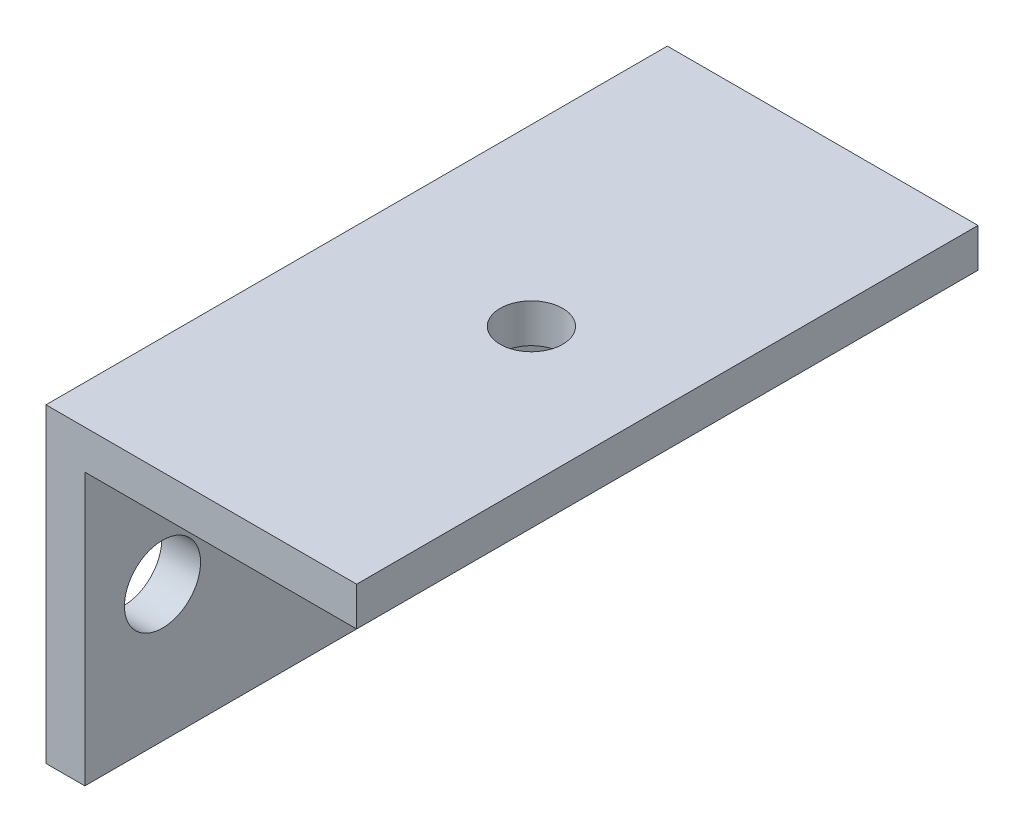
SolidWorks part; units mm, degrees
ref_plane "Front Plane" through (0, 0, 0) normal (0, 0, 1) x (1, 0, 0)
ref_plane "Top Plane" through (0, 0, 0) normal (0, 1, 0) x (1, 0, 0)
ref_plane "Right Plane" through (0, 0, 0) normal (1, 0, 0) x (0, 0, -1)
sketch "Sketch3" plane through (0, 0, 0) normal (0, 0, 1) x (1, 0, 0)
  line L0 (0, 0) -> (0, 25.4)
  line L1 (0, 25.4) -> (25.4, 25.4)
  line L2 (25.4, 25.4) -> (25.4, 22.225)
  line L3 (25.4, 22.225) -> (3.175, 22.225)
  line L4 (3.175, 22.225) -> (3.175, 0)
  line L5 (3.175, 0) -> (0, 0)
  dimension "D1" = 25.4
  dimension "D2" = 3.175
extrude "Boss-Extrude1" add sketch "Sketch3" along normal blind 50.8
sketch "Sketch6" plane through (3.175, 0, 0) normal (1, 0, 0) x (0, 0, -1)
  line L3 (-50.8, 11.1125) -> (0, 11.1125) construction
  line L4 (-50.8, 0) -> (-50.8, 22.225) construction
  line L5 (0, 0) -> (0, 22.225) construction
  circle A0 centre (-44.45, 11.1125) radius 3.1115
  circle A1 centre (-6.35, 11.1125) radius 3.1115
  dimension "D1" = 6.223
  dimension "D2" = 6.35
  dimension "D3" = 6.223
  dimension "D4" = 6.35
extrude "Cut-Extrude1" cut sketch "Sketch6" against normal through all
sketch "Sketch7" plane through (0, 22.225, 0) normal (0, -1, 0) x (-1, 0, 0)
  line L0 (-14.2875, -50.8) -> (-14.2875, 0) construction
  line L5 (-3.175, -50.8) -> (-25.4, -50.8) construction
  line L6 (-3.175, 0) -> (-25.4, 0) construction
hole_wizard "#10 Clearance Hole2" positions "Sketch9" profile "Sketch8" hole size "#10" standard "ANSI Inch" end condition through all
sketch "Sketch9" plane through (0, 22.225, 0) normal (0, -1, 0) x (-1, 0, 0)
  point P0 (-14.2875, -25.4)
  dimension "D1" = 25.4
sketch "Sketch8" plane through (14.2875, 22.225, 25.4) normal (1, 0, 0) x (0, 0, -1)
  line L0 (0, 0) -> (0, 3.175)
  line L1 (0, 3.175) -> (2.5527, 3.175)
  line L2 (2.5527, 3.175) -> (2.5527, 0)
  line L5 (2.5527, 0) -> (0, 0)
  line L11 (0, -6.35) -> (0, 107.95) construction
  dimension "Thru Hole Dia." = 5.1054
  dimension "Thru Hole Depth" = 3.175
